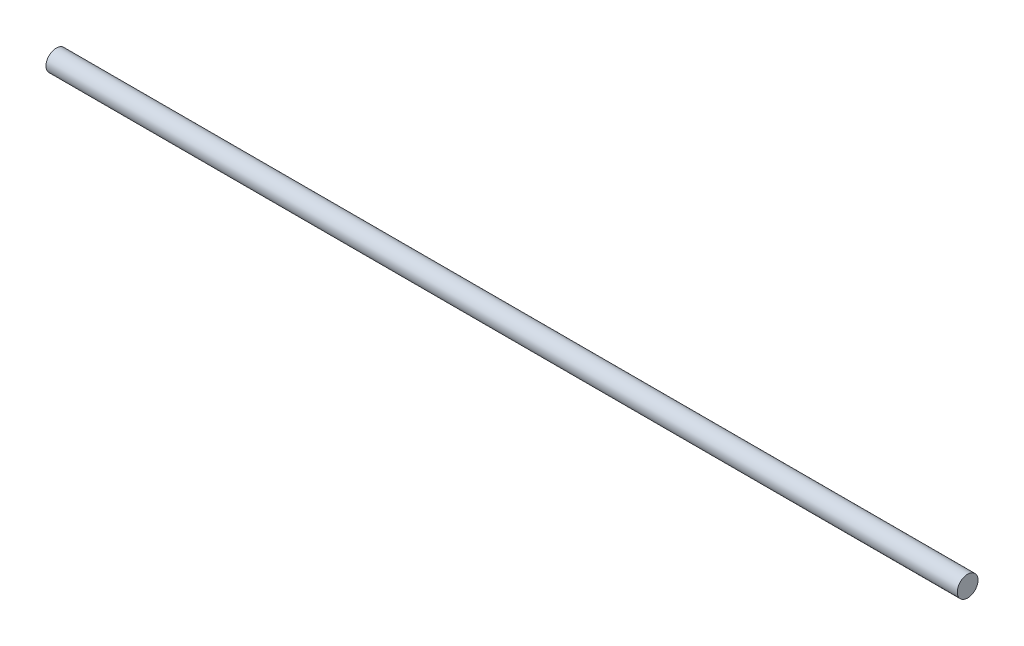
SolidWorks part; units mm, degrees
ref_plane "Piano frontale" through (0, 0, 0) normal (0, 0, 1) x (1, 0, 0)
ref_plane "Piano superiore" through (0, 0, 0) normal (0, 1, 0) x (1, 0, 0)
ref_plane "Piano destro" through (0, 0, 0) normal (1, 0, 0) x (0, 0, -1)
sketch "Schizzo1" plane through (0, 0, 0) normal (1, 0, 0) x (0, 0, -1)
  circle A1 centre (0, 0) radius 2.5
  circle A2 centre (0, 0) radius 2.5 construction
extrude "Estrusione-Estrusione1" add sketch "Schizzo1" along normal blind 220
